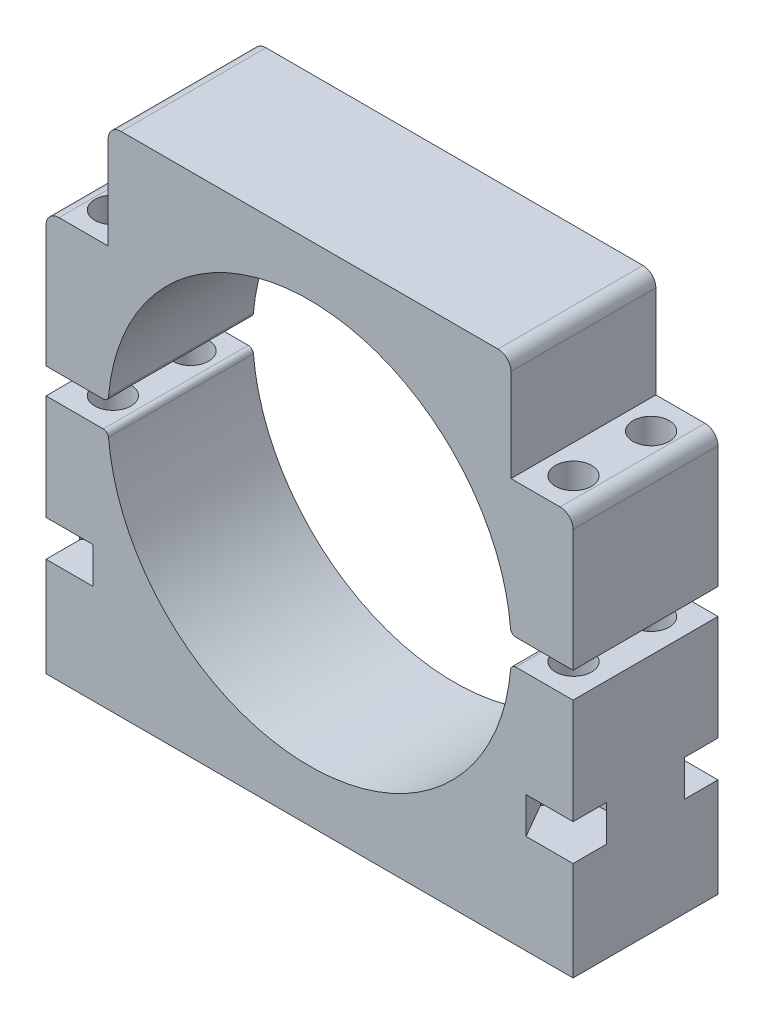
SolidWorks part; units mm, degrees
ref_plane "Front Plane" through (0, 0, 0) normal (0, 0, 1) x (1, 0, 0)
ref_plane "Top Plane" through (0, 0, 0) normal (0, 1, 0) x (1, 0, 0)
ref_plane "Right Plane" through (0, 0, 0) normal (1, 0, 0) x (0, 0, -1)
sketch "Sketch1" plane through (0, 0, 0) normal (0, 0, 1) x (1, 0, 0)
  line L0 (-38.9198, -2.5) -> (-50.9198, -2.5)
  line L1 (-50.9198, -2.5) -> (-50.9198, -49)
  line L2 (-50.9198, -49) -> (50.9198, -49)
  line L3 (50.9198, -49) -> (50.9198, -2.5)
  line L4 (50.9198, -2.5) -> (38.9198, -2.5)
  line L5 (0, 0) -> (0, -39) construction
  circle A0 centre (0, 0) radius 36 construction
  arc A1 (-38.9198, -2.5) -> (38.9198, -2.5) centre (0, 0) ccw
  dimension "D1" = 72
  dimension "D3" = 3
  dimension "D2" = 12
  dimension "D4" = 2.5
  dimension "D5" = 10
extrude "Boss-Extrude1" add sketch "Sketch1" along normal blind 28
sketch "Sketch2" plane through (0, 0, 0) normal (0, 0, 1) x (1, 0, 0)
  line L0 (50.9198, -2.5) -> (38.9198, -2.5) construction
  line L1 (-38.9198, -2.5) -> (-50.9198, -2.5) construction
  line L2 (50.9198, -2.5) -> (38.9198, -2.5) construction
  line L3 (-38.9198, -2.5) -> (-50.9198, -2.5) construction
  line L4 (0, 0) -> (36, 0) construction
  line L5 (-38.9198, 2.5) -> (-50.9198, 2.5)
  line L6 (50.9198, 2.5) -> (38.9198, 2.5)
  line L7 (-50.9198, 2.5) -> (-50.9198, 49)
  line L8 (-50.9198, 49) -> (50.9198, 49)
  line L9 (50.9198, 49) -> (50.9198, 2.5)
  line L10 (0, 0) -> (0, 39) construction
  arc A0 (-38.9198, -2.5) -> (38.9198, -2.5) centre (0, 0) ccw construction
  arc A1 (-38.9198, -2.5) -> (38.9198, -2.5) centre (0, 0) ccw construction
  circle A2 centre (0, 0) radius 36 construction
  arc A3 (-38.9198, 2.5) -> (38.9198, 2.5) centre (0, 0) cw
  dimension "D1" = 10
extrude "Boss-Extrude2" add sketch "Sketch2" along normal up to surface (28 mm away) separate body up to face at (0, -24.0833, 28)
ref_plane "Plane1" through (0, 28.575, 0) normal (0, 1, 0) x (1, 0, 0)
sketch "Sketch3" plane through (0, 28.575, 0) normal (0, 1, 0) x (1, 0, 0)
  line L0 (-44.504, -6.5) -> (-44.504, -21.5) construction
  line L1 (-50.9198, -28) -> (-50.9198, 0) construction
  line L3 (-50.9198, 0) -> (-38.9198, 0) construction
  line L4 (-50.9198, 0) -> (-38.9198, 0) construction
  line L7 (-50.9198, -6.5) -> (-47.7119, -12.0563) construction
  line L8 (-47.7119, -12.0563) -> (-41.2961, -12.0562) construction
  line L9 (-41.2961, -12.0562) -> (-38.0882, -6.5) construction
  line L10 (-38.0882, -6.5) -> (-41.2961, -0.9437) construction
  line L11 (-41.2961, -0.9437) -> (-47.7119, -0.9437) construction
  line L12 (-47.7119, -0.9437) -> (-50.9198, -6.5) construction
  circle A0 centre (-44.504, -6.5) radius 3.5
  circle A1 centre (-44.504, -21.5) radius 3.5
  circle A2 centre (-44.504, -6.5) radius 4.7625 construction
  circle A3 centre (-44.504, -21.5) radius 4.7625 construction
  circle A4 centre (-44.504, -6.5) radius 5.5562 construction
  point P4 (-44.504, -14)
  point P7 (-50.9198, -14)
  point P13 (-49.7578, -8.5494)
  point P21 (-48.6782, -6.5)
  dimension "D1" = 7
  dimension "D3" = 9.525
  dimension "D2" = 15
  dimension "D4" = 11.1125
extrude "Cut-Extrude1" cut sketch "Sketch3" against normal blind 58.42
fillet "Fillet1" radius 1 2 edges at (-38.9198, -2.5, 14) (38.9198, -2.5, 14)
fillet "Fillet2" radius 1 2 edges at (38.9198, 2.5, 14) (-38.9198, 2.5, 14)
sketch "Sketch4" plane through (0, 28.575, 0) normal (0, 1, 0) x (1, 0, 0)
  circle A0 centre (-44.504, -6.5) radius 4.7625 construction
  circle A1 centre (-44.504, -6.5) radius 4.7625 construction
  circle A2 centre (-44.504, -21.5) radius 4.7625 construction
  circle A3 centre (-44.504, -21.5) radius 4.7625 construction
  circle A4 centre (-44.504, -6.5) radius 5.2625
  circle A5 centre (-44.504, -21.5) radius 5.2625
  dimension "D1" = 0.5
extrude "Cut-Extrude2" [suppressed] cut sketch "Sketch4" along normal through all
sketch "Sketch5" plane through (0, 0, 0) normal (0, 0, 1) x (1, 0, 0)
  line L0 (15.4, 28.575) -> (-15.4, 28.575) construction
  line L1 (-50.9198, 49) -> (-38.9198, 49)
  line L2 (-50.9198, 49) -> (-50.9198, 28.575)
  line L3 (-50.9198, 28.575) -> (-38.9198, 28.575)
  line L4 (-38.9198, 49) -> (-38.9198, 28.575)
  line L5 (0, 0) -> (0, 49) construction
  line L6 (50.9198, 49) -> (-50.9198, 49) construction
  line L7 (38.9198, 49) -> (38.9198, 28.575)
  line L8 (50.9198, 28.575) -> (38.9198, 28.575)
  line L9 (50.9198, 49) -> (50.9198, 28.575)
  line L10 (50.9198, 49) -> (38.9198, 49)
  dimension "D1" = 12
extrude "Cut-Extrude3" cut sketch "Sketch5" against normal through all and the other way through all
fillet "Fillet3" radius 2.5 4 edges at (50.9198, 28.575, 14) (-50.9198, 28.575, 14) (38.9198, 49, 14) (-38.9198, 49, 14)
sketch "Sketch7" plane through (0, -29.845, 0) normal (0, 1, 0) x (1, 0, 0)
  line L0 (-38.0882, -6.5) -> (-41.2961, -0.9437) construction
  line L1 (-41.2961, -12.0562) -> (-38.0882, -6.5) construction
  line L2 (-47.7119, -12.0563) -> (-41.2961, -12.0562) construction
  line L4 (-38.0882, -6.5) -> (-41.2961, -0.9437)
  line L5 (-41.2961, -12.0562) -> (-38.0882, -6.5)
  line L6 (-47.7119, -12.0563) -> (-41.2961, -12.0562)
  line L7 (-50.9198, -6.5) -> (-47.7119, -12.0563) construction
  line L8 (-50.9198, -6.5) -> (-47.7119, -12.0563)
  line L9 (-50.9198, -6.5) -> (-50.9198, 0)
  line L10 (-50.9198, 0) -> (-41.841, 0)
  line L11 (-50.9198, 0) -> (50.9198, 0) construction
  line L12 (-41.841, 0) -> (-41.2961, -0.9437)
  line L13 (-38.9198, -14) -> (-50.9198, -14) construction
  line L14 (-38.9198, 0) -> (-38.9198, -28) construction
  line L15 (-50.9198, 0) -> (-50.9198, -28) construction
  line L16 (-50.9198, -28) -> (-41.841, -28)
  line L17 (-50.9198, -21.5) -> (-50.9198, -28)
  line L18 (-50.9198, -21.5) -> (-47.7119, -15.9437)
  line L19 (-47.7119, -15.9437) -> (-41.2961, -15.9437)
  line L20 (-41.2961, -15.9437) -> (-38.0882, -21.5)
  line L21 (-38.0882, -21.5) -> (-41.2961, -27.0563)
  line L22 (-41.841, -28) -> (-41.2961, -27.0563)
extrude "Cut-Extrude4" cut sketch "Sketch7" along normal blind 7
mirror "Mirror3" about plane through (0, 0, 0) normal (1, 0, 0) of "Cut-Extrude1", "Cut-Extrude4"
